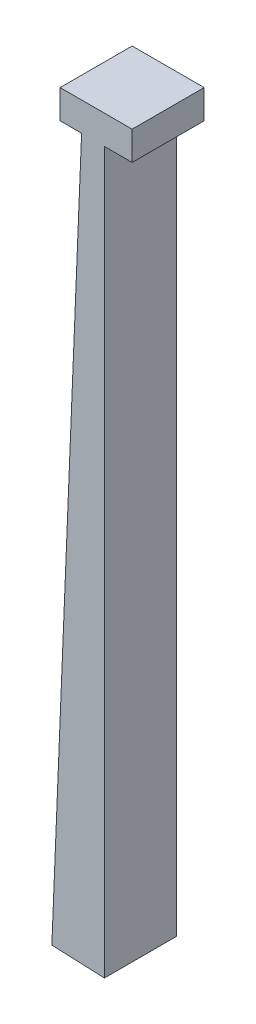
SolidWorks part; units mm, degrees
ref_plane "Front Plane" through (0, 0, 0) normal (0, 0, 1) x (1, 0, 0)
ref_plane "Top Plane" through (0, 0, 0) normal (0, 1, 0) x (1, 0, 0)
ref_plane "Right Plane" through (0, 0, 0) normal (1, 0, 0) x (0, 0, -1)
sketch "Sketch1" plane through (0, 0, 0) normal (0, 0, 1) x (1, 0, 0)
  line L0 (9.296, 93.7284) -> (-0.7862, 93.7284)
  line L1 (-15.704, 113.7284) -> (34.296, 113.7284)
  line L2 (-15.704, 113.7284) -> (-15.704, 93.7284)
  line L3 (-15.704, 93.7284) -> (34.296, 93.7284)
  line L4 (34.296, 113.7284) -> (34.296, 93.7284)
  line L5 (-0.7862, 93.7284) -> (-21.4487, -404.7585)
  line L6 (-21.4487, -404.7585) -> (15.0552, -406.2716)
  line L7 (15.0552, -406.2716) -> (15.0552, 93.7284)
extrude "Boss-Extrude1" add sketch "Sketch1" along normal blind 50 contours L6 L7 L3 L0 L5 | L4 L1 L2 L3 L0
